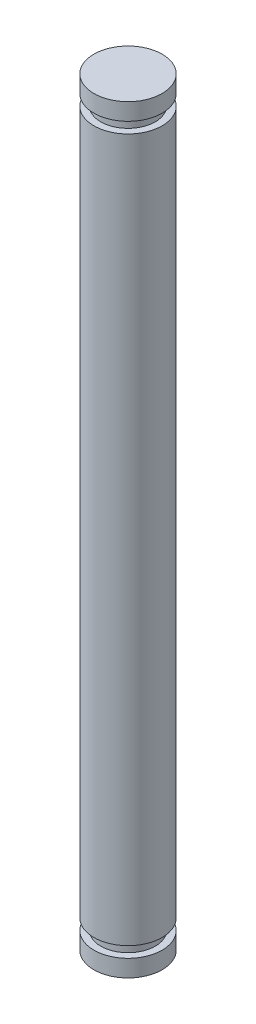
SolidWorks part; units mm, degrees
material "Plain Carbon Steel"
ref_plane "Front Plane" through (0, 0, 0) normal (0, 0, 1) x (1, 0, 0)
ref_plane "Top Plane" through (0, 0, 0) normal (0, 1, 0) x (1, 0, 0)
ref_plane "Right Plane" through (0, 0, 0) normal (1, 0, 0) x (0, 0, -1)
sketch "Sketch1" plane through (0, 0, 0) normal (0, 0, 1) x (1, 0, 0)
  line L0 (0, 0) -> (0, 33.6602) construction
  line L2 (0, 0) -> (2, 0)
  line L3 (0, 0) -> (0, 44.5)
  line L4 (0, 44.5) -> (2, 44.5)
  line L5 (2, 0) -> (2, 44.5)
  dimension "D1" = 44.5
  dimension "D2" = 4
revolve "Revolve1" add sketch "Sketch1" angle 360 about L0
sketch "Esquisse1" plane through (0, 0, 0) normal (0, 0, 1) x (1, 0, 0)
  line L0 (2, 44.5) -> (-2, 44.5) construction
  line L1 (2.1748, 43.5) -> (1.6, 43.5)
  line L2 (2.1748, 43.5) -> (2.1748, 42.86)
  line L3 (2.1748, 42.86) -> (1.6, 42.86)
  line L4 (1.6, 43.5) -> (1.6, 42.86)
  line L5 (0, 0) -> (0, 61.8456)
  dimension "D1" = 0.64
  dimension "D2" = 1
  dimension "D3" = 1.6
ref_axis "Axe1" through (0, 44.5, 0) along (0, -1, 0)
revolve "Enlèvement de matière-Révolution1" cut sketch "Esquisse1" angle 360 about axis through (0, 44.5, 0) along (0, -1, 0)
sketch "Esquisse2" plane through (0, 0, 0) normal (0, 0, 1) x (1, 0, 0)
  line L0 (2, 42.86) -> (-2, 42.86) construction
  line L1 (1.15, 28.76) -> (2.3294, 28.76)
  line L2 (1.15, 28.76) -> (1.15, 28.12)
  line L3 (1.15, 28.12) -> (2.3294, 28.12)
  line L4 (2.3294, 28.76) -> (2.3294, 28.12)
  line L5 (0, 44.5) -> (0, 0) construction
  dimension "D1" = 0.64
  dimension "D2" = 14.1
  dimension "D3" = 1.15
revolve "Enlèvement de matière-Révolution2" [suppressed] cut sketch "Esquisse2" angle 360 about axis through (0, 44.5, 0) along (0, -1, 0)
sketch "Esquisse3" plane through (0, 0, 0) normal (0, 0, 1) x (1, 0, 0)
  line L1 (1.6, 1.64) -> (2.6935, 1.64)
  line L2 (1.6, 1.64) -> (1.6, 1)
  line L3 (1.6, 1) -> (2.6935, 1)
  line L4 (2.6935, 1.64) -> (2.6935, 1)
  line L5 (0, 44.5) -> (0, 0) construction
  line L6 (-2, 0) -> (2, 0) construction
  dimension "D1" = 1
  dimension "D2" = 0.64
  dimension "D3" = 1.6
revolve "Enlèvement de matière-Révolution3" cut sketch "Esquisse3" angle 360 about axis through (0, 44.5, 0) along (0, -1, 0)
